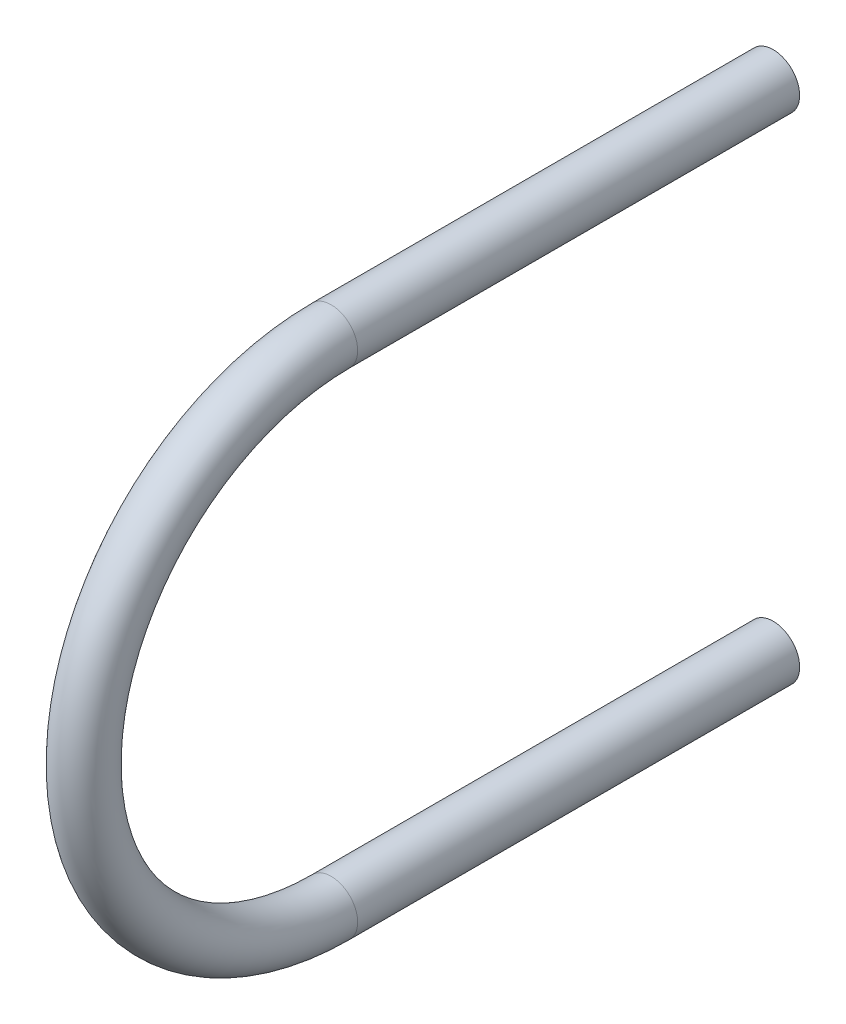
SolidWorks part; units mm, degrees
ref_plane "Спереди" through (0, 0, 0) normal (0, 0, 1) x (1, 0, 0)
ref_plane "Сверху" through (0, 0, 0) normal (0, 1, 0) x (1, 0, 0)
ref_plane "Справа" through (0, 0, 0) normal (1, 0, 0) x (0, 0, -1)
sketch "Эскиз1" plane through (0, 0, 0) normal (1, 0, 0) x (0, 0, -1)
  line L0 (0, 56) -> (50, 56)
  line L1 (0, 0) -> (0, 56) construction
  line L2 (0, 0) -> (50, 0)
  line L3 (50, 56) -> (50, 0) construction
  arc A0 (0, 0) -> (0, 56) centre (0, 28) cw
  dimension "D1" = 50
  dimension "D2" = 56
sweep "По траектории1" add path "Эскиз1" circular profile diameter 6 parameters "D3"=6
